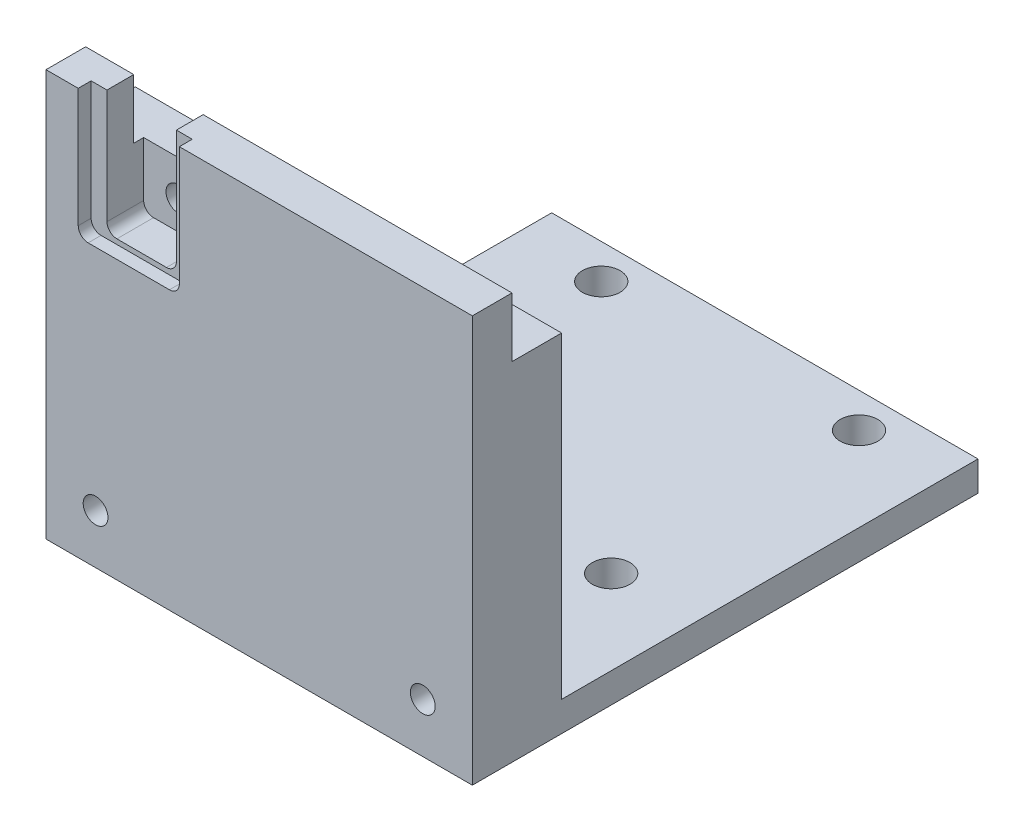
SolidWorks part; units mm, degrees
material "Ст 3 сп 5 ГОСТ 380-94"
ref_plane "Спереди" through (0, 0, 0) normal (0, 0, 1) x (1, 0, 0)
ref_plane "Сверху" through (0, 0, 0) normal (0, 1, 0) x (1, 0, 0)
ref_plane "Справа" through (0, 0, 0) normal (1, 0, 0) x (0, 0, -1)
sketch "Эскиз1" plane through (0, 0, 0) normal (0, 0, 1) x (1, 0, 0)
  line L1 (-21.5, 19) -> (21.5, 19)
  line L2 (-21.5, 19) -> (-21.5, -19)
  line L3 (-21.5, -19) -> (21.5, -19)
  line L4 (21.5, 19) -> (21.5, -19)
  line L5 (-21.5, 19) -> (21.5, -19) construction
  line L6 (-21.5, -19) -> (21.5, 19) construction
  point P0 (0, 0)
  dimension "D1" = 43
  dimension "D2" = 38
extrude "Бобышка-Вытянуть1" add sketch "Эскиз1" along normal blind 9
sketch "Эскиз2" plane through (0, 0, 9) normal (0, 0, 1) x (1, 0, 0)
  line L1 (-21.5, -19) -> (21.5, -19)
  line L2 (-21.5, -19) -> (-21.5, -22)
  line L3 (-21.5, -22) -> (21.5, -22)
  line L4 (21.5, -19) -> (21.5, -22)
  dimension "D1" = 43
  dimension "D2" = 3
extrude "Бобышка-Вытянуть3" add sketch "Эскиз2" against normal blind 51
sketch "Эскиз3" plane through (0, -22, 0) normal (0, -1, 0) x (1, 0, 0)
  line L0 (-21.5, -42) -> (21.5, -42) construction
  line L1 (-21.5, -42) -> (-21.5, 9) construction
  line L2 (21.5, -42) -> (21.5, 9) construction
  circle A0 centre (-13, -38.5) radius 1.9007
  circle A1 centre (13, -38.5) radius 1.9007
  circle A2 centre (13, -13.5) radius 1.9007
  circle A3 centre (-13, -13.5) radius 1.9007
  dimension "D1" = 3.5
  dimension "D2" = 8.5
  dimension "D5" = 8.5
  dimension "D3" = 2
  dimension "D4" = 2
extrude "Вырез-Вытянуть1" cut sketch "Эскиз3" against normal through all
sketch "Эскиз4" plane through (-21.5, 0, 0) normal (-1, 0, 0) x (0, 0, 1)
  line L0 (9, 19) -> (0, 19) construction
  line L1 (5, 19) -> (0, 19)
  line L2 (5, 19) -> (5, 13)
  line L3 (5, 13) -> (0, 13)
  line L4 (0, 19) -> (0, 13)
  line L5 (0, 19) -> (0, -19) construction
  dimension "D1" = 6
  dimension "D2" = 5
extrude "Вырез-Вытянуть2" cut sketch "Эскиз4" against normal through all
sketch "Эскиз7" plane through (0, 13, 0) normal (0, 1, 0) x (1, 0, 0)
  line L0 (21.5, 0) -> (21.5, -5) construction
  line L1 (21.5, -9) -> (-21.5, -9) construction
  circle A0 centre (16.5, -2.5) radius 1.2
  circle A1 centre (6.5, -2.5) radius 1.2
  circle A2 centre (-3.5, -2.5) radius 1.2
  dimension "D1" = 2.4
  dimension "D2" = 5
  dimension "D3" = 6.5
  dimension "D4" = 3
sketch "Эскиз8" plane through (0, 0, 9) normal (0, 0, 1) x (1, 0, 0)
  line L0 (-21.5, -22) -> (21.5, -22) construction
  line L1 (21.5, -22) -> (21.5, 19) construction
  circle A0 centre (16.5, -17) radius 1.25
  circle A1 centre (-16.5, -17) radius 1.25
  dimension "D1" = 2.5
  dimension "D2" = 5
  dimension "D3" = 5
  dimension "D4" = 2
extrude "Вырез-Вытянуть6" cut sketch "Эскиз8" against normal blind 9 contours A0
cosmetic thread "Условное изображение резьбы5" parameters "D2"=3
cosmetic thread "Условное изображение резьбы6" parameters "D2"=3
extrude "Вырез-Вытянуть7" cut sketch "Эскиз7" against normal blind 15
cosmetic thread "Условное изображение резьбы7" parameters "D2"=3
cosmetic thread "Условное изображение резьбы8" parameters "D2"=3
cosmetic thread "Условное изображение резьбы9" parameters "D2"=3
sketch "Эскиз9" plane through (0, 0, 9) normal (0, 0, 1) x (1, 0, 0)
  line L0 (21.5, 19) -> (-21.5, 19) construction
  line L1 (-8.05, 19) -> (-18.25, 19)
  line L2 (-8.05, 19) -> (-8.05, 6)
  line L3 (-8.05, 6) -> (-18.25, 6)
  line L4 (-18.25, 19) -> (-18.25, 6)
  line L5 (-21.5, 19) -> (-21.5, -22) construction
  dimension "D1" = 10.2
  dimension "D2" = 13
  dimension "D3" = 3.25
extrude "Вырез-Вытянуть8" cut sketch "Эскиз9" against normal blind 1.3
sketch "Эскиз10" plane through (0, 0, 7.7) normal (0, 0, 1) x (1, 0, 0)
  line L0 (-18.25, 6) -> (-8.05, 6) construction
  circle A0 centre (-13.15, 9.4) radius 1.25
  point P4 (-13.15, 6)
  dimension "D1" = 2.5
  dimension "D2" = 3.4
sketch "Эскиз11" plane through (0, 0, 7.7) normal (0, 0, 1) x (1, 0, 0)
  line L1 (-16.65, 6.5) -> (-9.65, 6.5)
  line L2 (-16.65, 6.5) -> (-16.65, 19)
  line L3 (-16.65, 19) -> (-9.65, 19)
  line L4 (-9.65, 6.5) -> (-9.65, 19)
  line L5 (-18.25, 19) -> (-18.25, 6) construction
  line L7 (-18.25, 6) -> (-8.05, 6) construction
  dimension "D1" = 7
  dimension "D2" = 1.6
  dimension "D3" = 0.5
extrude "Вырез-Вытянуть13" cut sketch "Эскиз11" against normal blind 3.7
extrude "Вырез-Вытянуть14" cut sketch "Эскиз10" against normal blind 8
fillet "Скругление1" radius 1 2 edges at (-9.65, 6.5, 5.85) (-16.65, 6.5, 5.85)
fillet "Скругление2" radius 1 2 edges at (-18.25, 6, 8.35) (-8.05, 6, 8.35)
